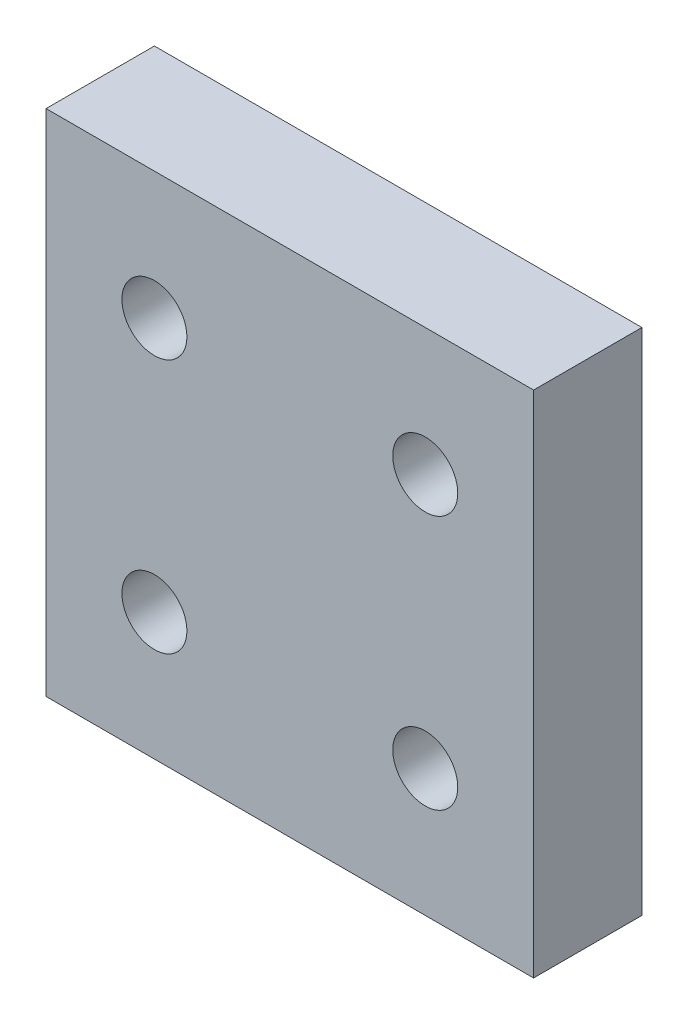
SolidWorks part; units mm, degrees
ref_plane "Plan de face" through (0, 0, 0) normal (0, 0, 1) x (1, 0, 0)
ref_plane "Plan de dessus" through (0, 0, 0) normal (0, 1, 0) x (1, 0, 0)
ref_plane "Plan de droite" through (0, 0, 0) normal (1, 0, 0) x (0, 0, -1)
sketch "Esquisse1" plane through (0, 0, 0) normal (0, 0, 1) x (1, 0, 0)
  line L1 (-9, 9.4) -> (9, 9.4)
  line L2 (-9, 9.4) -> (-9, -9.4)
  line L3 (-9, -9.4) -> (9, -9.4)
  line L4 (9, 9.4) -> (9, -9.4)
  line L5 (-9, 9.4) -> (9, -9.4) construction
  line L6 (-9, -9.4) -> (9, 9.4) construction
  line L7 (-5, 4.7) -> (5, 4.7) construction
  line L8 (-5, 4.7) -> (-5, -4.7) construction
  line L9 (-5, -4.7) -> (5, -4.7) construction
  line L10 (5, 4.7) -> (5, -4.7) construction
  line L11 (-5, 4.7) -> (5, -4.7) construction
  line L12 (-5, -4.7) -> (5, 4.7) construction
  circle A0 centre (-5, 4.7) radius 1.2
  circle A1 centre (5, 4.7) radius 1.2
  circle A2 centre (5, -4.7) radius 1.2
  circle A3 centre (-5, -4.7) radius 1.2
  point P0 (0, 0)
  point P6 (0, 0)
  dimension "D5" = 2.4
  dimension "D1" = 18.8
  dimension "D2" = 18
  dimension "D3" = 10
  dimension "D4" = 9.4
  dimension "D6" = 2
  dimension "D7" = 2
extrude "Boss.-Extru.1" add sketch "Esquisse1" along normal blind 4
